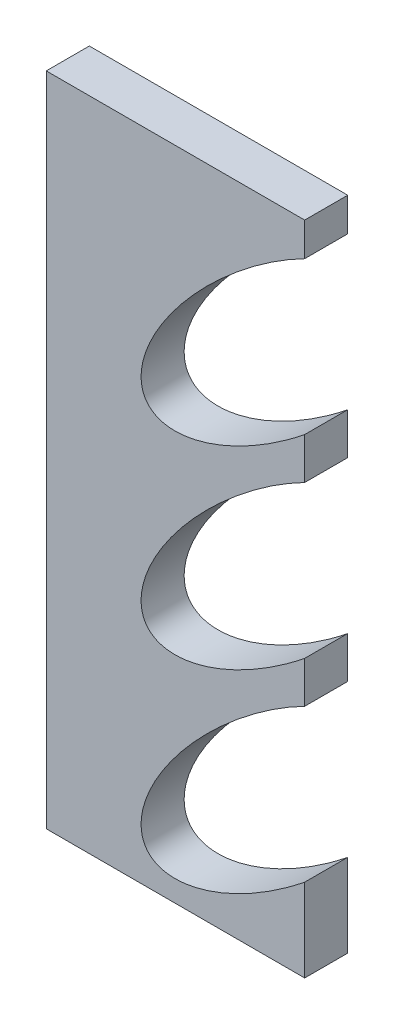
SolidWorks part; units mm, degrees
ref_plane "Front Plane" through (0, 0, 0) normal (0, 0, 1) x (1, 0, 0)
ref_plane "Top Plane" through (0, 0, 0) normal (0, 1, 0) x (1, 0, 0)
ref_plane "Right Plane" through (0, 0, 0) normal (1, 0, 0) x (0, 0, -1)
sketch "Sketch3" plane through (0, 0, 0) normal (0, 0, 1) x (1, 0, 0)
  line L1 (-41.1027, 45.4229) -> (18.8973, 45.4229)
  line L2 (-41.1027, 45.4229) -> (-41.1027, -106.9771)
  line L3 (-41.1027, -106.9771) -> (18.8973, -106.9771)
  line L4 (18.8973, 45.4229) -> (18.8973, -106.9771)
  ellipse E0 centre (11.5602, 15.145) end of major axis (40.7148, 39.9492) minor radius 14.5789
  ellipse E1 centre (11.5602, -29.855) end of major axis (40.7148, -5.0508) minor radius 14.5789
  ellipse E2 centre (11.5602, -74.855) end of major axis (-17.5943, -99.6592) minor radius 14.5789
  point P5 (0, 0)
  dimension "D1" = 60
  dimension "D2" = 152.4
  dimension "D3" = 3
extrude "Boss-Extrude7" add sketch "Sketch3" along normal blind 10 contours E2 L4 E1 E0 L1 L2 L3
